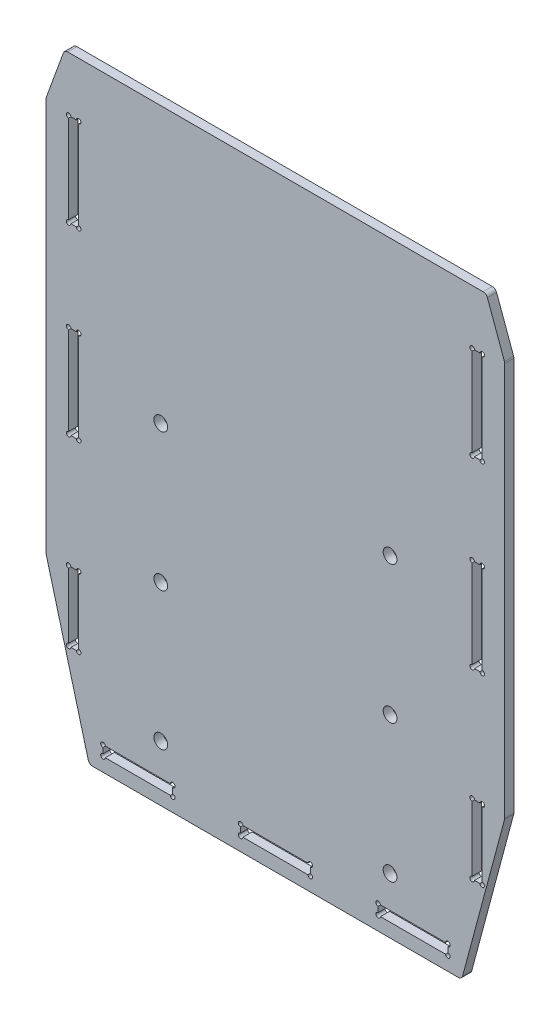
SolidWorks part; units mm, degrees
material "环氧板3240"
ref_plane "前视基准面" through (0, 0, 0) normal (0, 0, 1) x (1, 0, 0)
ref_plane "上视基准面" through (0, 0, 0) normal (0, 1, 0) x (1, 0, 0)
ref_plane "右视基准面" through (0, 0, 0) normal (1, 0, 0) x (0, 0, -1)
other "Configuration Table"
sketch "草图1" plane through (0, 0, 0) normal (0, 0, 1) x (1, 0, 0)
  line L0 (0, 76.1) -> (0, -76.1) construction
  line L1 (-50, 76.1) -> (50, 76.1)
  line L2 (-50, 76.1) -> (-50, -76.1)
  line L3 (-50, -76.1) -> (50, -76.1)
  line L4 (50, 76.1) -> (50, -76.1)
  line L5 (-50, 76.1) -> (50, -76.1) construction
  line L6 (-50, -76.1) -> (50, 76.1) construction
  line L7 (42.9, 24) -> (42.9, 4.2) construction
  line L8 (42.9, 44.2) -> (45.1, 44.2)
  line L9 (42.9, 44.2) -> (42.9, 24)
  line L10 (42.9, 24) -> (45.1, 24)
  line L11 (45.1, 44.2) -> (45.1, 24)
  line L12 (42.9, 44.2) -> (45.1, 24) construction
  line L13 (42.9, 24) -> (45.1, 44.2) construction
  line L14 (42.9, 4.2) -> (45.1, 4.2)
  line L15 (42.9, 4.2) -> (42.9, -16)
  line L16 (42.9, -16) -> (45.1, -16)
  line L17 (45.1, 4.2) -> (45.1, -16)
  line L18 (42.9, 4.2) -> (45.1, -16) construction
  line L19 (42.9, -16) -> (45.1, 4.2) construction
  line L20 (42.9, -40.8) -> (45.1, -40.8)
  line L21 (42.9, -40.8) -> (42.9, -56)
  line L22 (42.9, -56) -> (45.1, -56)
  line L23 (45.1, -40.8) -> (45.1, -56)
  line L24 (42.9, -40.8) -> (45.1, -56) construction
  line L25 (42.9, -56) -> (45.1, -40.8) construction
  line L26 (42.9, -16) -> (42.9, -40.8) construction
  line L27 (-42.9, -56) -> (-45.1, -56)
  line L28 (-45.1, -40.8) -> (-45.1, -56)
  line L29 (-42.9, -40.8) -> (-45.1, -40.8)
  line L30 (-42.9, -40.8) -> (-42.9, -56)
  line L31 (-42.9, -16) -> (-45.1, -16)
  line L32 (-45.1, 4.2) -> (-45.1, -16)
  line L33 (-42.9, 4.2) -> (-45.1, 4.2)
  line L34 (-42.9, 4.2) -> (-42.9, -16)
  line L35 (-42.9, 24) -> (-45.1, 24)
  line L36 (-45.1, 44.2) -> (-45.1, 24)
  line L37 (-42.9, 44.2) -> (-45.1, 44.2)
  line L38 (-42.9, 44.2) -> (-42.9, 24)
  line L39 (-50.3984, 56.1) -> (50.3984, 56.1)
  line L40 (-22.4, -70.9) -> (-7.6, -70.9) construction
  line L41 (-7.6, -73.1) -> (7.6, -73.1)
  line L42 (-7.6, -73.1) -> (-7.6, -70.9)
  line L43 (-7.6, -70.9) -> (7.6, -70.9)
  line L44 (7.6, -73.1) -> (7.6, -70.9)
  line L45 (-7.6, -73.1) -> (7.6, -70.9) construction
  line L46 (-7.6, -70.9) -> (7.6, -73.1) construction
  line L47 (-37.6, -73.1) -> (-22.4, -73.1)
  line L48 (-37.6, -73.1) -> (-37.6, -70.9)
  line L49 (-37.6, -70.9) -> (-22.4, -70.9)
  line L50 (-22.4, -73.1) -> (-22.4, -70.9)
  line L51 (-37.6, -73.1) -> (-22.4, -70.9) construction
  line L52 (-37.6, -70.9) -> (-22.4, -73.1) construction
  line L53 (22.4, -73.1) -> (37.6, -73.1)
  line L54 (22.4, -73.1) -> (22.4, -70.9)
  line L55 (22.4, -70.9) -> (37.6, -70.9)
  line L56 (37.6, -73.1) -> (37.6, -70.9)
  line L57 (22.4, -73.1) -> (37.6, -70.9) construction
  line L58 (22.4, -70.9) -> (37.6, -73.1) construction
  line L59 (7.6, -70.9) -> (22.4, -70.9) construction
  line L60 (50.3984, 56.1) -> (50, 56.1)
  line L61 (-50.3984, 56.1) -> (-50, 56.1)
  circle A3 centre (49.5, 31.1) radius 1.5 construction
  circle A4 centre (-49.5, 31.1) radius 1.5 construction
  circle A5 centre (0, 2.6) radius 73.5 construction
  point P4 (0, 0)
  point P11 (44, 34.1)
  point P16 (44, -5.9)
  point P21 (44, -48.4)
  point P42 (0, -72)
  point P47 (-30, -72)
  point P52 (30, -72)
  dimension "D13" = 3
  dimension "D16" = 45
  dimension "D17" = 15.2
  dimension "D7" = 147
  dimension "D14" = 99
  dimension "D1" = 20.2
  dimension "D2" = 2.2
  dimension "D3" = 19.8
  dimension "D4" = 31.9
  dimension "D5" = 85.8
  dimension "D6" = 100
  dimension "D8" = 15.2
  dimension "D9" = 3
  dimension "D10" = 14.8
  dimension "D11" = 20
  dimension "D12" = 2.2
  dimension "D15" = 24.8
extrude "凸台-拉伸1" add sketch "草图1" along normal blind 2 contours L39 L2 L3 L4 L8 L11 L10 L9 L14 L17 L16 L15 L20 L23 L22 L21 L29 L30 L27 L28 L33 L34 L31 L32 L37 L38 L35 L36 | L50 L3 L48 L49 | L44 L3 L42 L43 | L56 L3 L54 L55
sketch "草图3" plane through (0, 0, 0) normal (0, 0, -1) x (-1, 0, 0)
  line L2 (50, 45.1) -> (50, 56.1)
  line L3 (-50, 45.1) -> (-50, 56.1)
  line L5 (0, 56.1) -> (0, -76.1) construction
  line L6 (50, -76.1) -> (-50, -76.1) construction
  line L10 (-50, -41.1) -> (-40.6218, -76.1)
  line L11 (-40.6218, -76.1) -> (-50, -76.1)
  line L12 (-50, -76.1) -> (-50, -41.1)
  line L13 (40.6218, -76.1) -> (50, -76.1)
  line L14 (50, -41.1) -> (40.6218, -76.1)
  line L15 (50, -76.1) -> (50, -41.1)
  line L16 (45.9963, 56.1) -> (50, 45.1)
  line L17 (-50, 56.1) -> (-50, -76.1) construction
  line L18 (-50, 56.1) -> (-45.9963, 56.1)
  line L19 (-45.9963, 56.1) -> (-50, 45.1)
  line L20 (50, 56.1) -> (-50, 56.1) construction
  line L21 (50, 56.1) -> (45.9963, 56.1)
  dimension "D1" = 20
  dimension "D2" = 15
  dimension "D3" = 35
  dimension "D4" = 11
extrude "切除-拉伸1" cut sketch "草图3" against normal through all
sketch "草图4" plane through (0, 0, 2) normal (0, 0, 1) x (1, 0, 0)
  line L0 (0, 56.1) -> (0, -76.149) construction
  line L1 (-45.9963, 56.1) -> (45.9963, 56.1) construction
  line L2 (25, -63.9) -> (-25, -63.9) construction
  line L3 (-25, -3.9) -> (25, -3.9) construction
  line L4 (-25, -33.9) -> (25, -33.9) construction
  line L5 (25, -3.9) -> (25, -33.9) construction
  line L6 (-25, -63.9) -> (-25, -33.9) construction
  circle A0 centre (-25, -3.9) radius 1.5
  circle A1 centre (25, -3.9) radius 1.5
  circle A2 centre (-25, -33.9) radius 1.5
  circle A3 centre (25, -33.9) radius 1.5
  circle A4 centre (25, -63.9) radius 1.5
  circle A5 centre (-25, -63.9) radius 1.5
  dimension "D1" = 3
  dimension "D2" = 60
  dimension "D3" = 50
  dimension "D4" = 30
  dimension "D5" = 30
extrude "切除-拉伸2" cut sketch "草图4" against normal blind 10
sketch "草图2" plane through (0, 0, 2) normal (0, 0, 1) x (1, 0, 0)
  line L0 (-42.9, -56) -> (-45.1, -56) construction
  line L1 (-42.9, -40.8) -> (-42.9, -56) construction
  line L2 (0, 99.7783) -> (0, -76.1) construction
  line L4 (-40.6218, -76.1) -> (40.6218, -76.1) construction
  circle A0 centre (-45.1, 44.2) radius 0.5
  circle A1 centre (-42.9, 44.2) radius 0.5
  circle A2 centre (-45.1, 24) radius 0.5
  circle A3 centre (-42.9, 24) radius 0.5
  circle A4 centre (-45.1, 4.2) radius 0.5
  circle A5 centre (-42.9, 4.2) radius 0.5
  circle A6 centre (-45.1, -16) radius 0.5
  circle A7 centre (-42.9, -16) radius 0.5
  circle A8 centre (-45.1, -40.8) radius 0.5
  circle A9 centre (-42.9, -40.8) radius 0.5
  circle A10 centre (-45.1, -56) radius 0.5
  circle A11 centre (-42.9, -56) radius 0.5
  circle A12 centre (-37.6, -70.9) radius 0.5
  circle A13 centre (-37.6, -73.1) radius 0.5
  circle A14 centre (-22.4, -70.9) radius 0.5
  circle A15 centre (-22.4, -73.1) radius 0.5
  circle A16 centre (-7.6, -70.9) radius 0.5
  circle A17 centre (-7.6, -73.1) radius 0.5
  circle A18 centre (7.6, -73.1) radius 0.5
  circle A19 centre (7.6, -70.9) radius 0.5
  circle A20 centre (22.4, -73.1) radius 0.5
  circle A21 centre (22.4, -70.9) radius 0.5
  circle A22 centre (37.6, -73.1) radius 0.5
  circle A23 centre (37.6, -70.9) radius 0.5
  circle A24 centre (42.9, -56) radius 0.5
  circle A25 centre (45.1, -56) radius 0.5
  circle A26 centre (42.9, -40.8) radius 0.5
  circle A27 centre (45.1, -40.8) radius 0.5
  circle A28 centre (42.9, -16) radius 0.5
  circle A29 centre (45.1, -16) radius 0.5
  circle A30 centre (42.9, 4.2) radius 0.5
  circle A31 centre (45.1, 4.2) radius 0.5
  circle A32 centre (42.9, 24) radius 0.5
  circle A33 centre (45.1, 24) radius 0.5
  circle A34 centre (42.9, 44.2) radius 0.5
  circle A35 centre (45.1, 44.2) radius 0.5
  dimension "D1" = 1
extrude "切除-拉伸3" cut sketch "草图2" against normal through all contours A4
fillet "圆角1" radius 1 8 edges at (-45.9963, 56.1, 1) (-50, 45.1, 1) (-50, -41.1, 1) (-40.6218, -76.1, 1) (40.6218, -76.1, 1) (50, -41.1, 1) (50, 45.1, 1) (45.9963, 56.1, 1)
